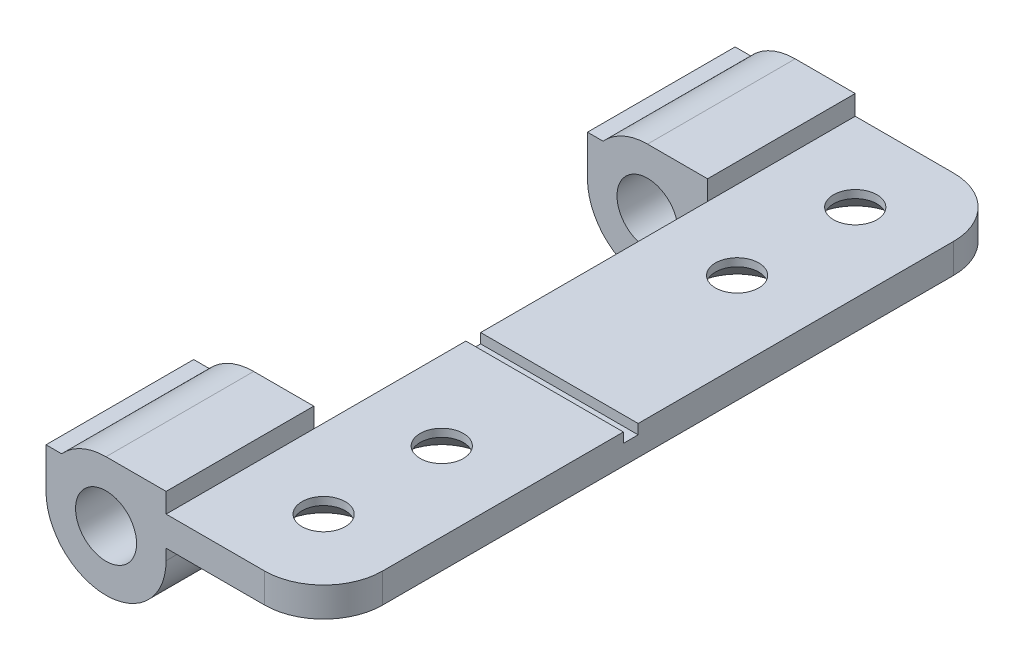
SolidWorks part; units mm, degrees
material "6061-T6 (SS)"
ref_plane "Front Plane" through (0, 0, 0) normal (0, 0, 1) x (1, 0, 0)
ref_plane "Top Plane" through (0, 0, 0) normal (0, 1, 0) x (1, 0, 0)
ref_plane "Right Plane" through (0, 0, 0) normal (1, 0, 0) x (0, 0, -1)
sketch "Sketch2" plane through (0, 0, 0) normal (0, 0, 1) x (1, 0, 0)
  line L0 (3.05, 2.05) -> (11.05, 2.05)
  line L1 (11.05, 2.05) -> (11.05, 0.55)
  line L2 (11.05, 0.55) -> (3.05, 0.55)
  line L3 (0, 1.55) -> (15.0271, 1.55) construction
  line L4 (3.05, 2.05) -> (3.05, 3.05)
  line L5 (3.05, 3.05) -> (0, 3.05)
  line L6 (3.05, 0) -> (3.05, 0.55)
  line L7 (-3.05, 0) -> (-3.05, 2.05)
  line L8 (-3.05, 2.05) -> (-2.2583, 2.05)
  circle A0 centre (0, 0) radius 1.55
  arc A1 (0, 3.05) -> (-2.2583, 2.05) centre (0, 0) ccw
  arc A2 (-3.05, 0) -> (3.05, 0) centre (0, 0) ccw
  dimension "D1" = 3.1
  dimension "D2" = 1.5
  dimension "D3" = 1.5
  dimension "D4" = 8
  dimension "D5" = 0.5
extrude "Boss-Extrude1" add sketch "Sketch2" along normal blind 7.5
sketch "Sketch4" plane through (0, 0, 7.5) normal (0, 0, 1) x (1, 0, 0)
  line L1 (11.05, 2.05) -> (3.05, 2.05)
  line L2 (11.05, 2.05) -> (11.05, 0.55)
  line L3 (11.05, 0.55) -> (3.05, 0.55)
  line L4 (3.05, 2.05) -> (3.05, 0.55)
  line L5 (11.05, 2.05) -> (3.05, 0.55) construction
  line L6 (11.05, 0.55) -> (3.05, 2.05) construction
  point P4 (7.05, 1.3)
extrude "Boss-Extrude3" add sketch "Sketch4" along normal blind 20
sketch "Sketch5" plane through (0, 0, 27.5) normal (0, 0, 1) x (1, 0, 0)
  line L0 (11.05, 0.55) -> (11.05, 2.05) construction
  line L1 (11.05, 2.05) -> (3.05, 2.05) construction
  line L3 (3.05, 0.55) -> (11.05, 0.55) construction
  line L5 (3.05, 2.05) -> (3.05, 3.05) construction
  line L6 (3.05, 3.05) -> (0, 3.05) construction
  line L7 (3.05, 0) -> (3.05, 0.55) construction
  line L8 (11.05, 0.55) -> (11.05, 2.05)
  line L9 (11.05, 2.05) -> (3.05, 2.05)
  line L11 (3.05, 0.55) -> (11.05, 0.55)
  line L13 (3.05, 2.05) -> (3.05, 3.05)
  line L14 (3.05, 3.05) -> (0, 3.05)
  line L15 (3.05, 0) -> (3.05, 0.55)
  line L16 (-2.2583, 2.05) -> (-3.05, 2.05) construction
  line L17 (-3.05, 2.05) -> (-3.05, 0) construction
  line L18 (-2.2583, 2.05) -> (-3.05, 2.05)
  line L19 (-3.05, 2.05) -> (-3.05, 0)
  circle A1 centre (0, 0) radius 1.55 construction
  circle A3 centre (0, 0) radius 1.55
  arc A4 (0, 3.05) -> (-2.2583, 2.05) centre (0, 0) ccw construction
  arc A5 (-3.05, 0) -> (3.05, 0) centre (0, 0) ccw construction
  arc A6 (0, 3.05) -> (-2.2583, 2.05) centre (0, 0) ccw
  arc A7 (-3.05, 0) -> (3.05, 0) centre (0, 0) ccw
extrude "Boss-Extrude4" add sketch "Sketch5" along normal blind 7.5
sketch "Sketch6" plane through (3.05, 0, 0) normal (-1, 0, 0) x (0, 0, 1)
  line L0 (27.5, 2.05) -> (7.5, 2.05) construction
  line L1 (19.775, 2.05) -> (19.025, 2.05)
  line L2 (19.775, 2.05) -> (19.775, 1.55)
  line L3 (19.775, 1.55) -> (19.025, 1.55)
  line L4 (19.025, 2.05) -> (19.025, 1.55)
  line L5 (19.775, 2.05) -> (19.025, 1.55) construction
  line L6 (19.775, 1.55) -> (19.025, 2.05) construction
  point P4 (19.4, 1.8)
  dimension "D1" = 0.5
  dimension "D2" = 0.75
  dimension "D3" = 7.725
extrude "Cut-Extrude1" cut sketch "Sketch6" against normal through all
sketch "Sketch7" plane through (0, 0.55, 0) normal (0, -1, 0) x (1, 0, 0)
  line L0 (7.05, 35) -> (7.05, 0) construction
  line L1 (3.05, 35) -> (11.05, 35) construction
  line L2 (3.05, 0) -> (11.05, 0) construction
  line L3 (11.05, 35) -> (11.05, 0) construction
  circle A0 centre (7.05, 25) radius 1.1
  circle A1 centre (7.05, 10) radius 1.1
  circle A2 centre (7.05, 31) radius 1.1
  circle A3 centre (7.05, 4) radius 1.1
  dimension "D6" = 2.2
  dimension "D1" = 35
  dimension "D2" = 15
  dimension "D3" = 6
  dimension "D4" = 6
  dimension "D5" = 10
extrude "Cut-Extrude2" cut sketch "Sketch7" against normal through all
chamfer "Chamfer1" distance 1.1 angle 45 4 edges at (8.15, 0.55, 31) (8.15, 0.55, 25) (8.15, 0.55, 10) (8.15, 0.55, 4)
fillet "Fillet1" radius 3 2 edges at (11.05, 1.3, 0) (11.05, 1.3, 35)
equation "\"D4@Sketch7\"=\"D3@Sketch7\""
equation "\"D5@Sketch7\"=(\"D1@Sketch7\"-\"D2@Sketch7\")/2"
